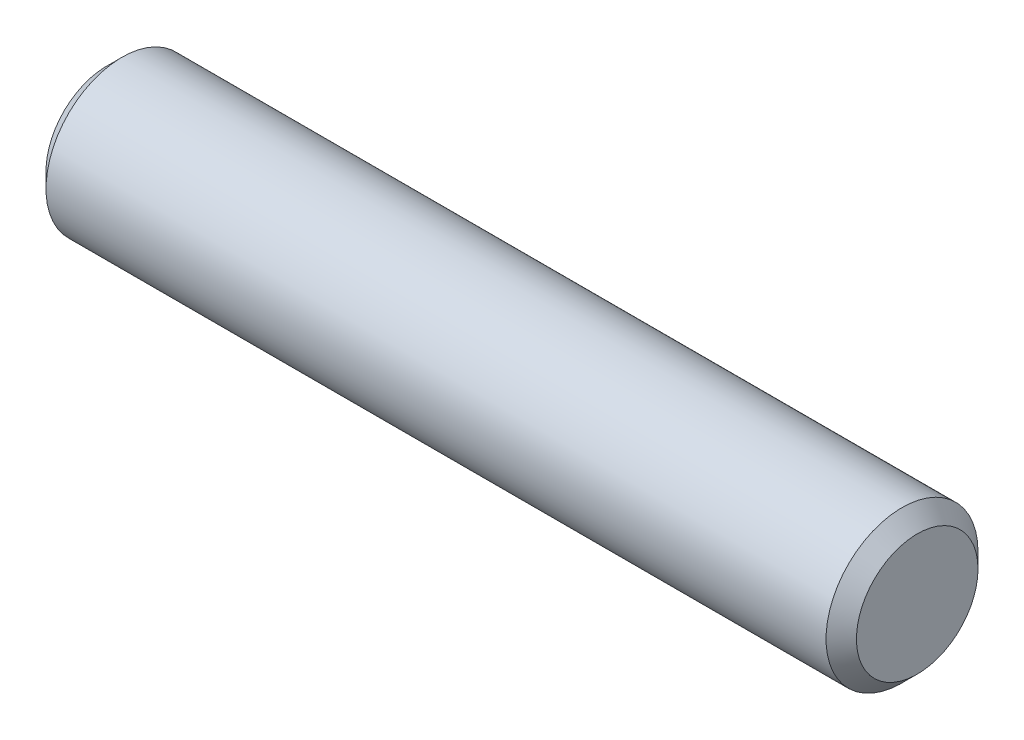
SolidWorks part; units mm, degrees
ref_plane "Front" through (0, 0, 0) normal (0, 0, 1) x (1, 0, 0)
ref_plane "Top" through (0, 0, 0) normal (0, 1, 0) x (1, 0, 0)
ref_plane "Right" through (0, 0, 0) normal (1, 0, 0) x (0, 0, -1)
sketch "Sketch1" plane through (0, 0, 0) normal (0, 0, 1) x (1, 0, 0)
  line L0 (-6.35, 0) -> (6.35, 0) construction
  line L1 (6.35, 1.1906) -> (6.35, -1.1906) construction
  line L2 (-6.35, 1.1906) -> (-6.35, -1.1906) construction
  dimension "Length" = 12.7
  dimension "Diameter" = 2.3813
sketch "Sketch2" plane through (0, 0, 0) normal (1, 0, 0) x (0, 0, -1)
  circle A0 centre (0, 0) radius 1.1906
extrude "Extrude1" add sketch "Sketch2" against normal up to vertex (6.35 mm away) and the other way up to vertex (6.35 mm away) up to point (-6.35, 1.1906, 0) other way up to point (6.35, 1.1906, 0)
chamfer "Chamfer1" distance 0.2381 angle 45 2 edges at (6.35, 0, -1.1906) (-6.35, 0, -1.1906)
equation "\"D1@Chamfer1\" = \"Diameter@Sketch1\"*.1"
